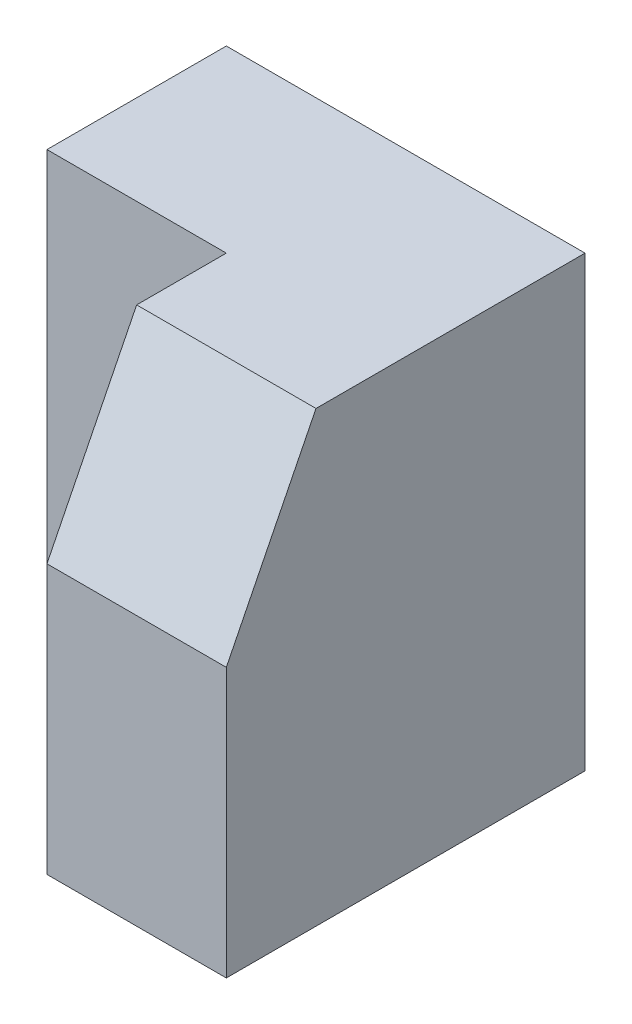
SolidWorks part; units mm, degrees
ref_plane "Front Plane" through (0, 0, 0) normal (0, 0, 1) x (1, 0, 0)
ref_plane "Top Plane" through (0, 0, 0) normal (0, 1, 0) x (1, 0, 0)
ref_plane "Right Plane" through (0, 0, 0) normal (1, 0, 0) x (0, 0, -1)
sketch "Sketch1" plane through (0, 0, 0) normal (0, 0, 1) x (1, 0, 0)
  line L1 (0, 0) -> (30, 0)
  line L2 (0, 0) -> (0, 25)
  line L3 (0, 25) -> (30, 25)
  line L4 (30, 0) -> (30, 25)
  dimension "D1" = 30
  dimension "D2" = 25
extrude "Boss-Extrude1" add sketch "Sketch1" along normal blind 20
sketch "Sketch2" plane through (0, 0, 20) normal (0, 0, 1) x (1, 0, 0)
  line L0 (30, 25) -> (0, 25) construction
  line L1 (0, 0) -> (20, 0)
  line L2 (0, 0) -> (0, 25)
  line L3 (0, 25) -> (20, 25)
  line L4 (20, 0) -> (20, 25)
  dimension "D1" = 20
extrude "Cut-Extrude1" cut sketch "Sketch2" against normal blind 10
sketch "Sketch3" plane through (20, 0, 0) normal (-1, 0, 0) x (0, 0, 1)
  line L0 (15, 25) -> (20, 15)
  line L1 (10, 25) -> (20, 25) construction
  line L2 (20, 0) -> (20, 25) construction
  line L3 (20, 15) -> (20, 25)
  line L4 (20, 25) -> (15, 25)
  dimension "D1" = 5
  dimension "D2" = 10
extrude "Cut-Extrude2" cut sketch "Sketch3" against normal blind 20
sketch "Sketch4" plane through (0, 25, 0) normal (0, 1, 0) x (1, 0, 0)
  line L0 (0, -10) -> (10, -10)
  line L1 (20, -10) -> (0, -10) construction
  line L2 (10, -10) -> (0, 0)
  line L3 (0, 0) -> (0, -10)
  dimension "D1" = 10
extrude "Cut-Extrude3" cut sketch "Sketch4" against normal blind 40
sketch "Sketch5" plane through (0, 0, 10) normal (0, 0, 1) x (1, 0, 0)
  line L0 (10, 25) -> (10, 0) construction
  line L1 (0, 25) -> (10, 25)
  line L2 (0, 25) -> (0, 14.9983)
  line L3 (0, 14.9983) -> (10, 14.9983)
  line L4 (10, 25) -> (10, 14.9983)
extrude "Cut-Extrude4" cut sketch "Sketch5" against normal blind 20
